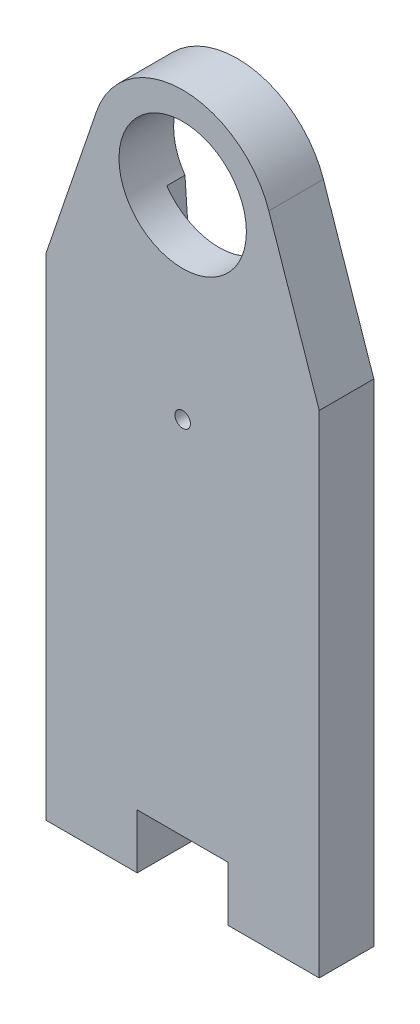
SolidWorks part; units mm, degrees
ref_plane "Alzado" through (0, 0, 0) normal (0, 0, 1) x (1, 0, 0)
ref_plane "Planta" through (0, 0, 0) normal (0, 1, 0) x (1, 0, 0)
ref_plane "Vista lateral" through (0, 0, 0) normal (1, 0, 0) x (0, 0, -1)
sketch "Corte exterior" plane through (0, 0, 0) normal (0, 0, 1) x (1, 0, 0)
  line L0 (40.5, 11.75) -> (35.5, 11.75)
  line L1 (35.5, 11.75) -> (35.5, 38.75)
  line L2 (35.5, 38.75) -> (38.2677, 46.8642)
  line L3 (47.7323, 46.8642) -> (50.5, 38.75)
  line L4 (50.5, 38.75) -> (50.5, 24.75)
  line L5 (50.5, 24.75) -> (50.5, 11.75)
  line L6 (50.5, 11.75) -> (45.5, 11.75)
  line L7 (45.5, 11.75) -> (45.5, 14.75)
  line L8 (45.5, 14.75) -> (40.5, 14.75)
  line L9 (40.5, 14.75) -> (40.5, 11.75)
  circle A0 centre (43, 34.5778) radius 0.425
  circle A1 centre (43, 45.25) radius 3.5
  arc A2 (47.7323, 46.8642) -> (38.2677, 46.8642) centre (43, 45.25) ccw
sketch "Grabado Superficie" plane through (0, 0, 0) normal (0, 0, 1) x (1, 0, 0)
  line L0 (41.0048, 30.6112) -> (40.125, 43.2539)
  line L1 (45.875, 43.2539) -> (44.9952, 30.6112)
  arc A0 (40.125, 43.2539) -> (45.875, 43.2539) centre (43, 45.25) ccw
  arc A1 (41.0048, 30.6112) -> (44.9952, 30.6112) centre (43, 30.75) ccw
extrude "Saliente-Extruir3" add sketch "Corte exterior" along normal blind 3
extrude "Cortar-Extruir2" cut sketch "Grabado Superficie" along normal blind 1
